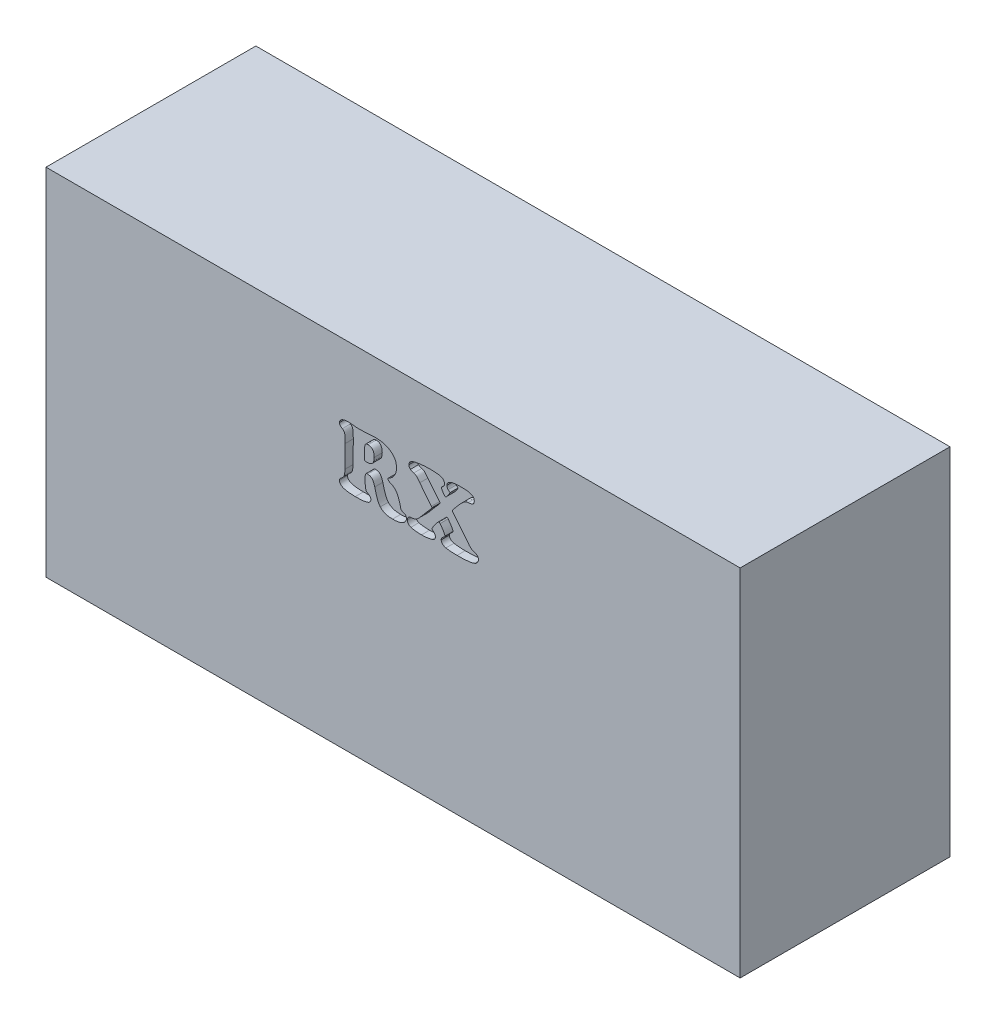
SolidWorks part; units mm, degrees
material "uhlíková ocel 7850"
ref_plane "Přední rovina" through (0, 0, 0) normal (0, 0, 1) x (1, 0, 0)
ref_plane "Horní rovina" through (0, 0, 0) normal (0, 1, 0) x (1, 0, 0)
ref_plane "Pravá rovina" through (0, 0, 0) normal (1, 0, 0) x (0, 0, -1)
sketch "Skica1" plane through (0, 0, 0) normal (0, 0, 1) x (1, 0, 0)
  line L1 (21.5, -11) -> (-21.5, -11)
  line L2 (21.5, -11) -> (21.5, 11)
  line L3 (21.5, 11) -> (-21.5, 11)
  line L4 (-21.5, -11) -> (-21.5, 11)
  line L5 (21.5, -11) -> (-21.5, 11) construction
  line L6 (21.5, 11) -> (-21.5, -11) construction
  point P0 (0, 0)
  dimension "D1" = 43
  dimension "D2" = 22
extrude "Přidat vysunutím1" add sketch "Skica1" along normal blind 13
sketch "Skica2" plane through (0, 0, 13) normal (0, 0, 1) x (1, 0, 0)
  text T0 "RX" font "Cooper Black" height in points 16
extrude "Odebrat vysunutím1" cut sketch "Skica2" against normal blind 0.5
